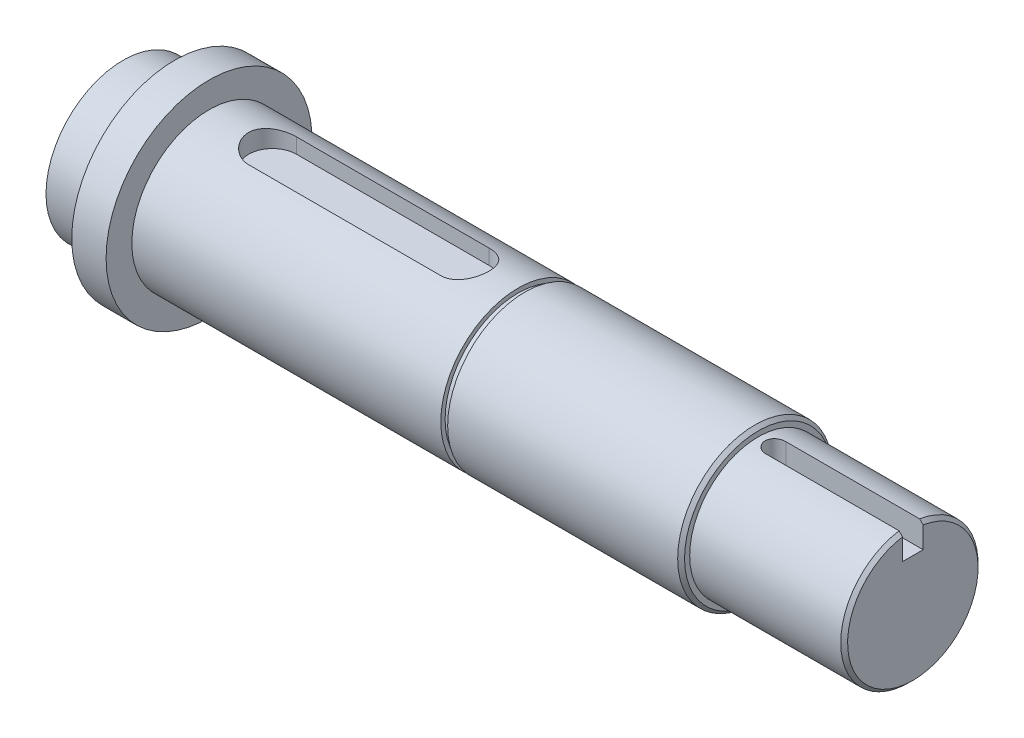
SolidWorks part; units mm, degrees
material "11 600"
ref_plane "Přední rovina" through (0, 0, 0) normal (0, 0, 1) x (1, 0, 0)
ref_plane "Vrchní rovina" through (0, 0, 0) normal (0, 1, 0) x (1, 0, 0)
ref_plane "Pravá rovina" through (0, 0, 0) normal (1, 0, 0) x (0, 0, -1)
sketch "Skica1" plane through (0, 0, 0) normal (0, 0, 1) x (1, 0, 0)
  line L0 (-258.8054, 0) -> (342.5626, 0) construction
  line L1 (0, 0) -> (0, 22.5)
  line L2 (0, 22.5) -> (15, 22.5)
  line L3 (15, 22.5) -> (15, 30)
  line L4 (15, 30) -> (25, 30)
  line L5 (25, 30) -> (25, 22.5)
  line L6 (25, 22.5) -> (115, 22.5)
  line L7 (115, 22.5) -> (115, 21.25)
  line L8 (115, 21.25) -> (117, 21.25)
  line L9 (117, 21.25) -> (117, 22.5)
  line L10 (117, 22.5) -> (185, 22.5)
  line L11 (185, 22.5) -> (185, 20)
  line L12 (185, 20) -> (230, 20)
  line L13 (230, 20) -> (230, 0)
  line L14 (0, 0) -> (230, 0)
  dimension "D1" = 230
  dimension "D2" = 45
  dimension "D3" = 60
  dimension "D4" = 15
  dimension "D5" = 10
  dimension "D6" = 90
  dimension "D7" = 2
  dimension "D8" = 70
  dimension "D9" = 40
  dimension "D10" = 42.5
revolve "Rotovat1" add sketch "Skica1" angle 360 about L0
cosmetic thread "Kosmetický závit1" parameters "D1"=42, "D2"=34.61
chamfer "Zkosení1" distance 1 2 edges at (185, 0, 22.5) (230, 0, 20)
ref_plane "Rovina2" through (0, 20, 0) normal (0, 1, 0) x (1, 0, 0)
sketch "Skica6" plane through (0, 20, 0) normal (0, 1, 0) x (1, 0, 0)
  line L0 (230, 0) -> (190, 0) construction
  line L1 (230, -3) -> (190, -3)
  line L2 (230, 3) -> (190, 3)
  line L3 (230, -20) -> (230, 20) construction
  arc A0 (230, -3) -> (230, 3) centre (230, 0) ccw
  arc A1 (190, 3) -> (190, -3) centre (190, 0) ccw
  point P3 (210, 0)
  dimension "D1" = 40
  dimension "D2" = 6
extrude "Odebrat vysunutím1" cut sketch "Skica6" against normal blind 7.5
ref_plane "Rovina3" through (0, 22.5, 0) normal (0, 1, 0) x (1, 0, 0)
sketch "Skica7" plane through (0, 22.5, 0) normal (0, 1, 0) x (1, 0, 0)
  line L0 (43.5, 0) -> (99.5, 0) construction
  line L1 (43.5, 7) -> (99.5, 7)
  line L2 (43.5, -7) -> (99.5, -7)
  line L4 (25, -22.5) -> (25, 22.5) construction
  arc A0 (43.5, 7) -> (43.5, -7) centre (43.5, 0) ccw
  arc A1 (99.5, -7) -> (99.5, 7) centre (99.5, 0) ccw
  point P3 (71.5, 0)
  dimension "D3" = 70
  dimension "D1" = 14
  dimension "D2" = 11.5
extrude "Odebrat vysunutím2" cut sketch "Skica7" against normal blind 5.5
